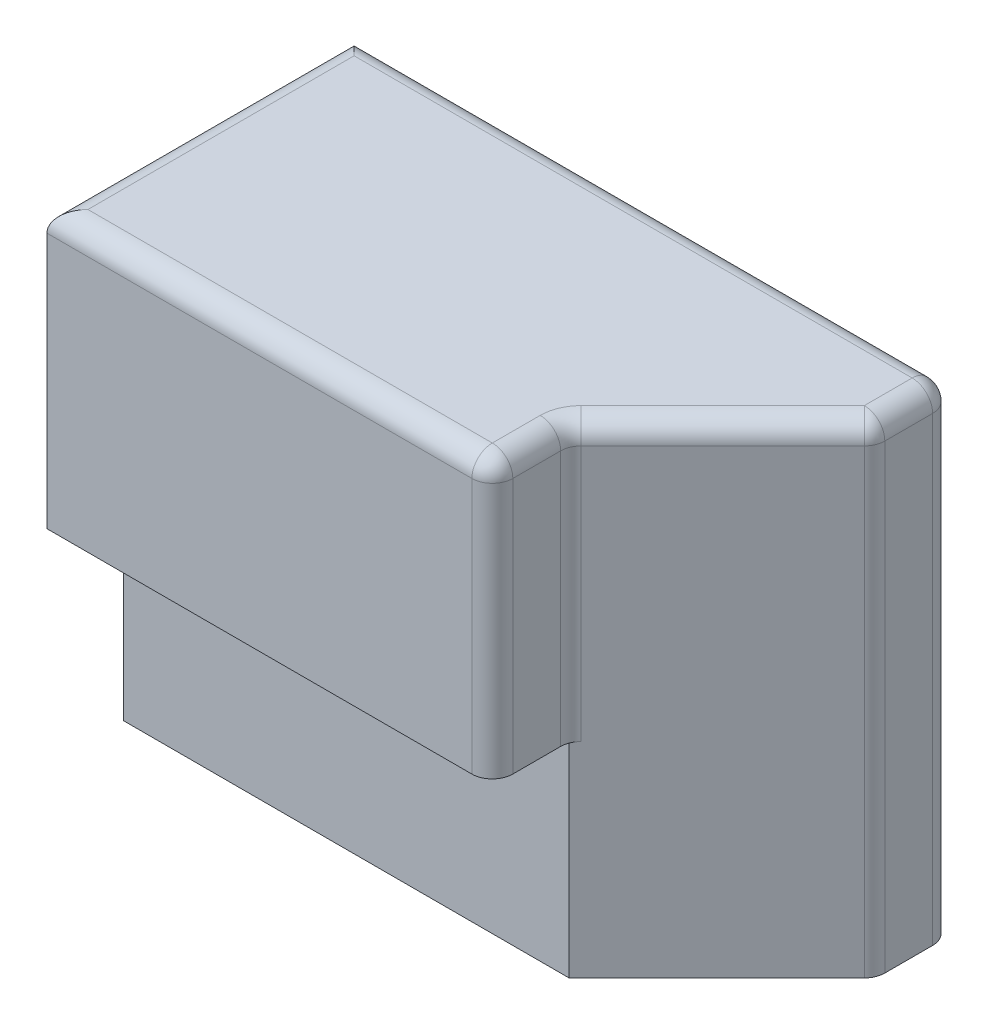
SolidWorks part; units mm, degrees
ref_plane "Front Plane" through (0, 0, 0) normal (0, 0, 1) x (1, 0, 0)
ref_plane "Top Plane" through (0, 0, 0) normal (0, 1, 0) x (1, 0, 0)
ref_plane "Right Plane" through (0, 0, 0) normal (1, 0, 0) x (0, 0, -1)
sketch "Sketch2" plane through (0, 0, 0) normal (0, 0, 1) x (1, 0, 0)
  line L1 (0, 0) -> (14.859, 0)
  line L2 (0, 0) -> (0, 11.938)
  line L3 (0, 11.938) -> (14.859, 11.938)
  line L4 (14.859, 0) -> (14.859, 11.938)
  dimension "D1" = 11.938
  dimension "D2" = 14.859
extrude "Boss-Extrude1" add sketch "Sketch2" along normal blind 7.62
sketch "Sketch4" plane through (0, 0, 0) normal (0, 0, -1) x (-1, 0, 0)
  line L1 (0, 0) -> (-10.16, 0)
  line L2 (0, 0) -> (0, 10.16)
  line L3 (0, 10.16) -> (-8.255, 10.16)
  line L4 (-10.16, 0) -> (-10.16, 8.255)
  arc A0 (-8.255, 10.16) -> (-10.16, 8.255) centre (-8.255, 8.255) ccw
  dimension "D3" = 1.905
  dimension "D1" = 10.16
  dimension "D2" = 10.16
extrude "Cut-Extrude2" cut sketch "Sketch4" against normal blind 2.794
sketch "Sketch5" plane through (0, 0, 7.62) normal (0, 0, 1) x (1, 0, 0)
  line L1 (0, 11.938) -> (11.049, 11.938)
  line L2 (0, 11.938) -> (0, 5.08)
  line L3 (0, 5.08) -> (11.049, 5.08)
  line L4 (0, 11.938) -> (0, 0)
  line L5 (0, 0) -> (14.859, 0)
  line L6 (14.859, 0) -> (14.859, 11.938)
  line L7 (14.859, 11.938) -> (0, 11.938)
  line L8 (0, 11.938) -> (0, 0)
  line L9 (0, 0) -> (14.859, 0)
  line L10 (14.859, 0) -> (14.859, 11.938)
  line L11 (14.859, 11.938) -> (0, 11.938)
  line L12 (11.049, 11.938) -> (11.049, 5.08)
  line M7 (0, 11.938) -> (0, 0)
  line M8 (0, 0) -> (14.859, 0)
  line M9 (14.859, 0) -> (14.859, 11.938)
  line M10 (14.859, 11.938) -> (0, 11.938)
  dimension "D2" = 5.08
  dimension "D3" = 3.81
  dimension "D1" = 0
extrude "Cut-Extrude3" cut sketch "Sketch5" against normal blind 1.905 contours L12 L3 M10 M7 M8 M9
sketch "Sketch6" plane through (0, 11.938, 0) normal (0, 1, 0) x (1, 0, 0)
  line L0 (11.049, -5.715) -> (14.859, -1.905)
  line L6 (0, -7.62) -> (11.049, -7.62)
  line L7 (11.049, -7.62) -> (11.049, -5.715)
  line L8 (11.049, -5.715) -> (14.859, -5.715)
  line L9 (14.859, -5.715) -> (14.859, 0)
  line L10 (14.859, 0) -> (0, 0)
  line L11 (0, 0) -> (0, -7.62)
  line L12 (0, -7.62) -> (11.049, -7.62)
  line L13 (11.049, -7.62) -> (11.049, -5.715)
  line L14 (11.049, -5.715) -> (14.859, -5.715)
  line L15 (14.859, -5.715) -> (14.859, 0)
  line L16 (14.859, 0) -> (0, 0)
  line L17 (0, 0) -> (0, -7.62)
  line M10 (11.049, -5.715) -> (14.859, -5.715)
  line M11 (14.859, -5.715) -> (14.859, 0)
  dimension "D2" = 45
  dimension "D1" = 0
extrude "Cut-Extrude4" cut sketch "Sketch6" against normal through all contours L0 M10 M11
fillet "Fillet1" radius 0.508 10 edges at (11.049, 11.938, 6.6675) (14.859, 5.969, 0) (0, 11.938, 3.81) (7.4295, 11.938, 0) (14.859, 11.938, 0.9525) (14.859, 5.969, 1.905) (12.954, 11.938, 3.81) (11.049, 8.509, 5.715) (11.049, 8.509, 7.62) (5.5245, 11.938, 7.62)
sketch "Sketch7" plane through (0, 0, 2.794) normal (0, 0, -1) x (-1, 0, 0)
  line L4 (0, 0) -> (0, 10.16) construction
  line L5 (-10.16, 0) -> (0, 0) construction
  circle A1 centre (-3.81, 3.81) radius 0.635
  dimension "D1" = 3.81
  dimension "D2" = 1.27
  dimension "D3" = 3.81
extrude "Cut-Extrude13" cut sketch "Sketch7" against normal blind 1.905
